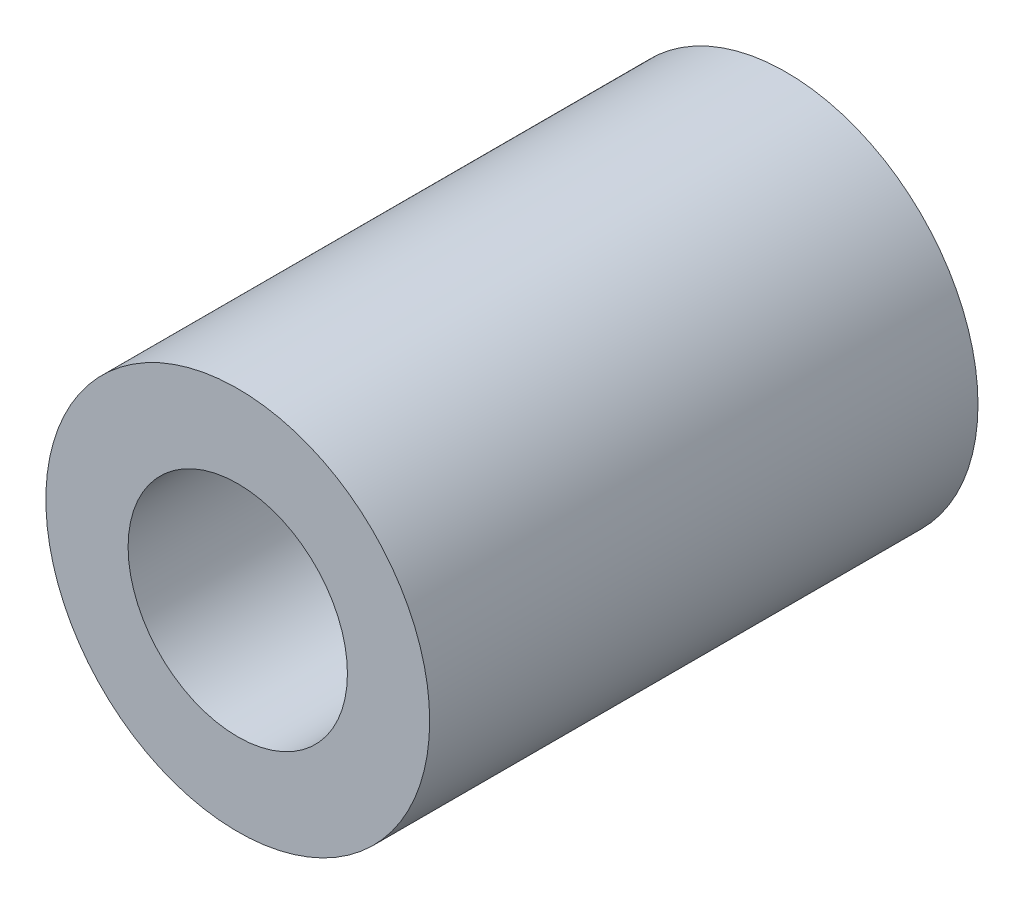
SolidWorks part; units mm, degrees
ref_plane "前视基准面" through (0, 0, 0) normal (0, 0, 1) x (1, 0, 0)
ref_plane "上视基准面" through (0, 0, 0) normal (0, 1, 0) x (1, 0, 0)
ref_plane "右视基准面" through (0, 0, 0) normal (1, 0, 0) x (0, 0, -1)
sketch "草图1" plane through (0, 0, 0) normal (0, 0, 1) x (1, 0, 0)
  circle A0 centre (0, 0) radius 3
  circle A1 centre (0, 0) radius 7
extrude "凸台-拉伸1" add sketch "草图1" along normal blind 10
sketch "草图2" plane through (0, 0, 10) normal (0, 0, 1) x (1, 0, 0)
  circle A0 centre (0, 0) radius 7
extrude "凸台-拉伸2" add sketch "草图2" along normal blind 10
sketch "草图3" plane through (0, 0, 20) normal (0, 0, 1) x (1, 0, 0)
  circle A0 centre (0, 0) radius 4
extrude "切除-拉伸1" cut sketch "草图3" against normal blind 8
